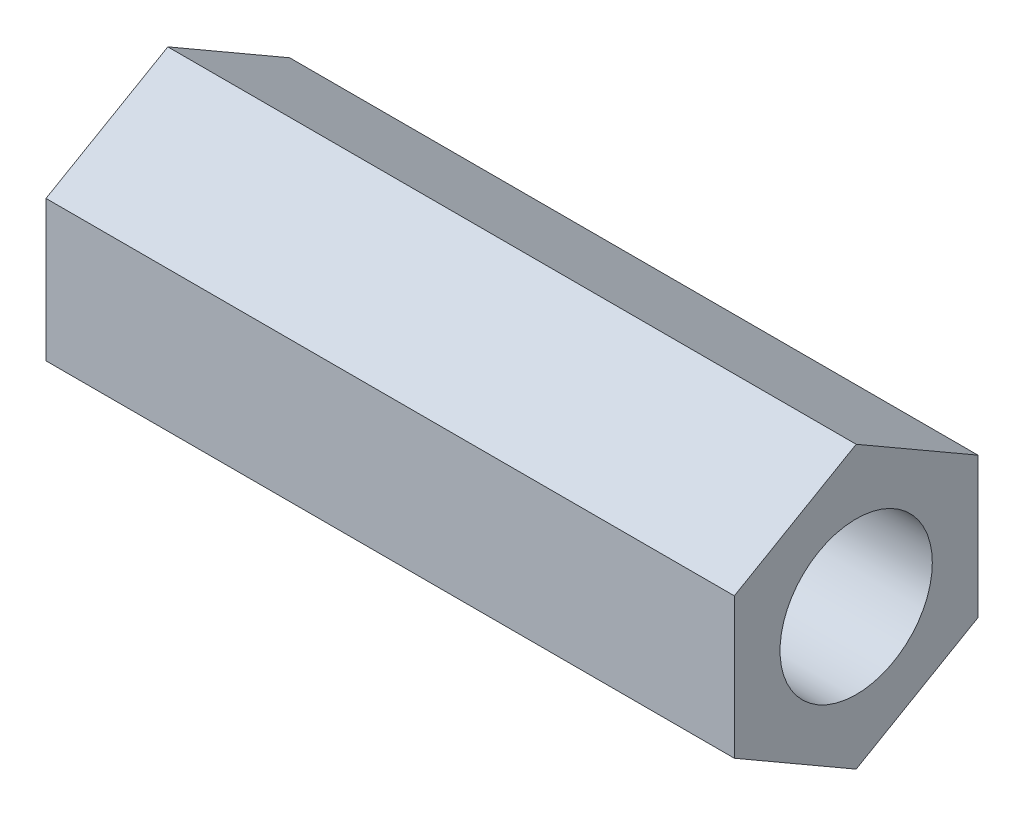
SolidWorks part; units mm, degrees
ref_plane "Front Plane" through (0, 0, 0) normal (0, 0, 1) x (1, 0, 0)
ref_plane "Top Plane" through (0, 0, 0) normal (0, 1, 0) x (1, 0, 0)
ref_plane "Right Plane" through (0, 0, 0) normal (1, 0, 0) x (0, 0, -1)
sketch "Sketch1" plane through (0, 0, 0) normal (1, 0, 0) x (0, 0, -1)
  line L1 (0, 4.6188) -> (-4, 2.3094)
  line L2 (-4, 2.3094) -> (-4, -2.3094)
  line L3 (-4, -2.3094) -> (0, -4.6188)
  line L4 (0, -4.6188) -> (4, -2.3094)
  line L5 (4, -2.3094) -> (4, 2.3094)
  line L6 (4, 2.3094) -> (0, 4.6188)
  circle A0 centre (0, 0) radius 4 construction
  circle A1 centre (0, 0) radius 2.5
  dimension "D1" = 5
  dimension "D2" = 8
extrude "Boss-Extrude1" add sketch "Sketch1" along normal blind 22.6
